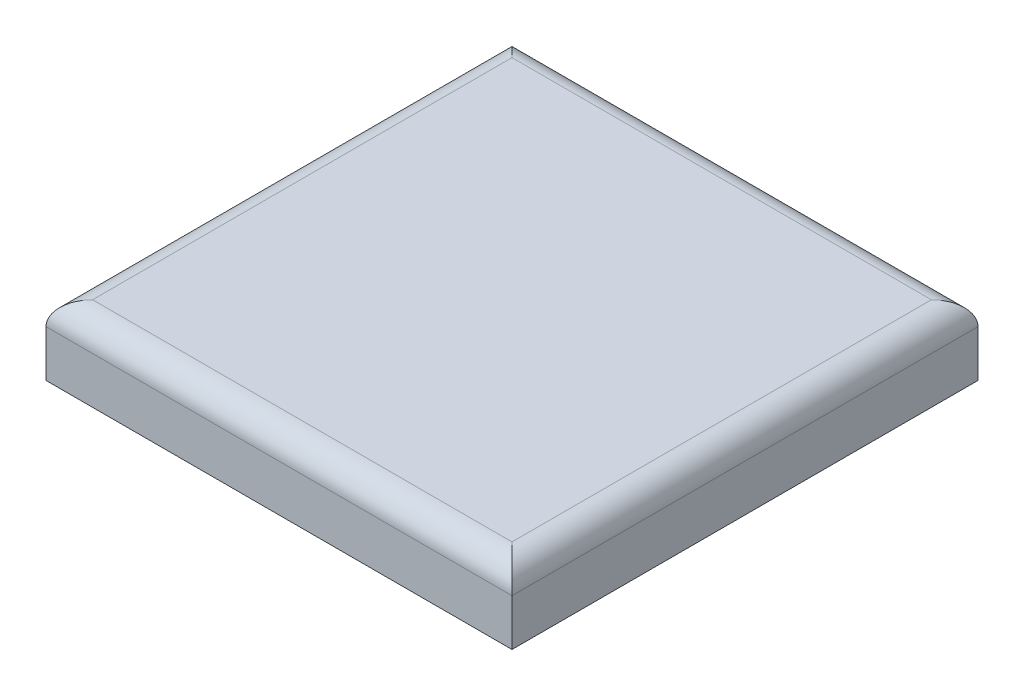
SolidWorks part; units mm, degrees
material "ABS"
ref_plane "Ön Düzlem" through (0, 0, 0) normal (0, 0, 1) x (1, 0, 0)
ref_plane "Üst Düzlem" through (0, 0, 0) normal (0, 1, 0) x (1, 0, 0)
ref_plane "Sağ Düzlem" through (0, 0, 0) normal (1, 0, 0) x (0, 0, -1)
sketch "Sketch1" plane through (0, 0, 0) normal (0, 1, 0) x (1, 0, 0)
  line L1 (-10, 10) -> (10, 10)
  line L2 (-10, 10) -> (-10, -10)
  line L3 (-10, -10) -> (10, -10)
  line L4 (10, 10) -> (10, -10)
  line L5 (-10, 10) -> (10, -10) construction
  line L6 (-10, -10) -> (10, 10) construction
  point P0 (0, 0)
  dimension "D1" = 20
extrude "Boss-Extrude1" add sketch "Sketch1" along normal blind 3
fillet "Fillet1" radius 1 4 edges at (-10, 3, 0) (0, 3, -10) (10, 3, 0) (0, 3, 10)
sketch "Sketch2" plane through (0, 0, 0) normal (0, -1, 0) x (1, 0, 0)
  circle A0 centre (0, 0) radius 2.5
  dimension "D1" = 5
extrude "Boss-Extrude2" add sketch "Sketch2" along normal blind 5
